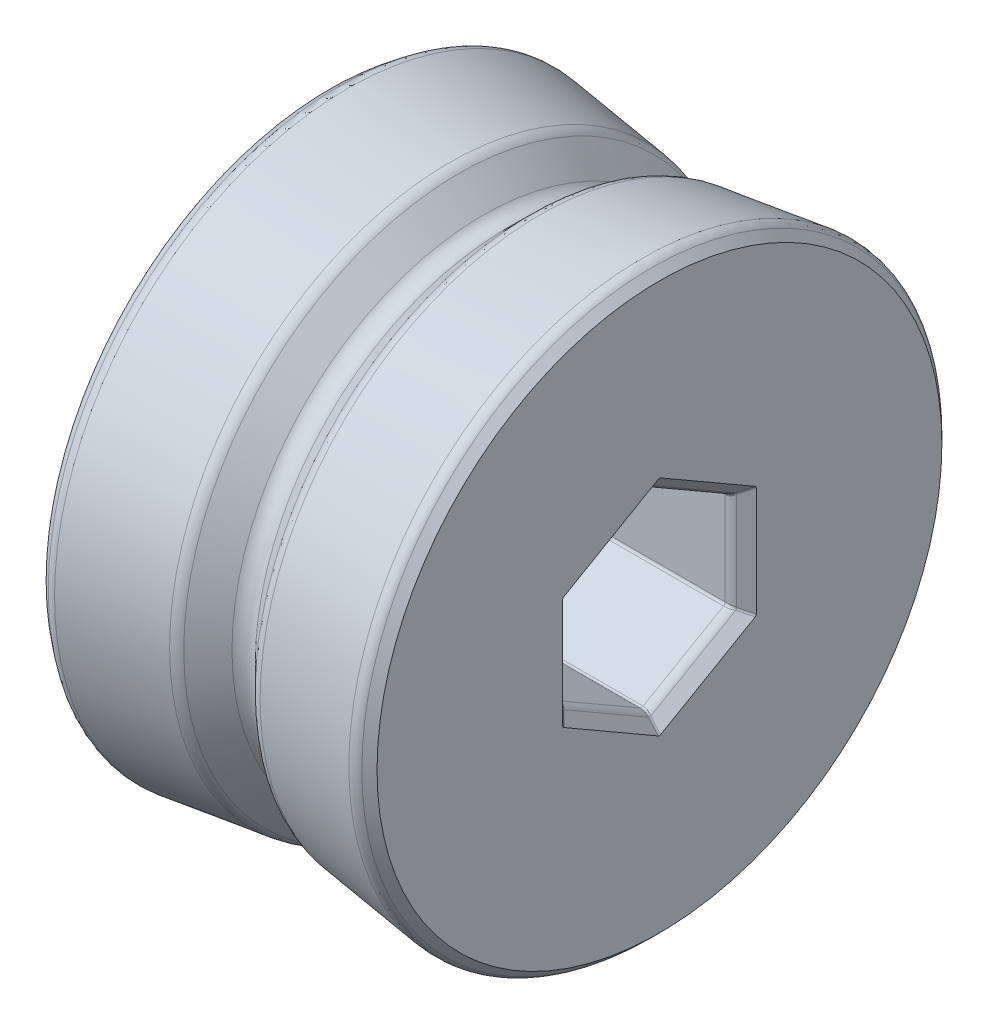
SolidWorks part; units mm, degrees
ref_plane "Front Plane" through (0, 0, 0) normal (0, 0, 1) x (1, 0, 0)
ref_plane "Top Plane" through (0, 0, 0) normal (0, 1, 0) x (1, 0, 0)
ref_plane "Right Plane" through (0, 0, 0) normal (1, 0, 0) x (0, 0, -1)
sketch "Sketch1" plane through (0, 0, 0) normal (0, 0, 1) x (1, 0, 0)
  line L0 (0, 0) -> (25.4, 0) construction
  line L1 (0, 0) -> (0, 22.7877)
  line L2 (0, 22.7877) -> (9.2118, 21.5749)
  line L3 (9.944, 21.2138) -> (11.802, 19.3558)
  line L4 (13.598, 19.3558) -> (15.456, 21.2138)
  line L5 (16.1882, 21.5749) -> (25.4, 22.7877)
  line L6 (25.4, 22.7877) -> (25.4, 0)
  line L7 (0, 22.7877) -> (25.4, 22.7877) construction
  line L8 (0, 0) -> (25.4, 0)
  circle A0 centre (12.7, 21.7805) radius 2.3495 construction
  arc A1 (15.456, 21.2138) -> (16.1882, 21.5749) centre (16.354, 20.3158) cw
  arc A2 (9.2118, 21.5749) -> (9.944, 21.2138) centre (9.046, 20.3158) cw
  arc A3 (11.802, 19.3558) -> (13.598, 19.3558) centre (12.7, 20.2539) ccw
  point P3 (12.7, 0)
  point P9 (12.7, 24.13)
  point P10 (0, 23.9923)
  point P11 (12.7, 19.7278)
  point P12 (25.4, 24.3537)
  point P13 (0, 0)
  point P16 (0, 0)
  point P17 (25.4, 22.9684)
  point P18 (9.9682, 21.1896)
  point P19 (0, 26.2811)
  point P20 (0, 0)
  point P21 (25.4, 22.7877)
  point P24 (15.7608, 21.5186)
  point P27 (9.6392, 21.5186)
  dimension "D1" = 4.699
  dimension "D5" = 1.27
  dimension "D2" = 25.4
  dimension "D3" = 24.13
  dimension "D4" = 82.5
revolve "Revolve1" add sketch "Sketch1" angle 360 about L8
sketch "Sketch2" plane through (25.4, 0, 0) normal (1, 0, 0) x (0, 0, -1)
  line L1 (6.45, -3.7239) -> (6.45, 3.7239)
  line L2 (6.45, 3.7239) -> (0, 7.4478)
  line L3 (0, 7.4478) -> (-6.45, 3.7239)
  line L4 (-6.45, 3.7239) -> (-6.45, -3.7239)
  line L5 (-6.45, -3.7239) -> (0, -7.4478)
  line L6 (0, -7.4478) -> (6.45, -3.7239)
  circle A0 centre (0, 0) radius 6.45 construction
  point P1 (6.45, 0)
  point P10 (0, 7.4478)
  dimension "D1" = 12.9
extrude "Cut-Extrude1" cut sketch "Sketch2" against normal through all both and the other way through all
chamfer "Chamfer1" distance 1.016 angle 45 14 edges at (0, 0, 6.45) (0, 5.5859, 3.225) (0, 5.5859, -3.225) (0, 0, -6.45) (0, -5.5859, -3.225) (0, -5.5859, 3.225) (25.4, 5.5859, -3.225) (25.4, 5.5859, 3.225) (25.4, 0, 6.45) (25.4, -5.5859, 3.225) (25.4, -5.5859, -3.225) (25.4, 0, -6.45) (0, 0, 22.7877) (25.4, 0, 22.7877)
fillet "Fillet2" radius 0.889 14 edges at (1.016, -5.5859, -3.225) (1.016, 0, -6.45) (1.016, 5.5859, -3.225) (1.016, 5.5859, 3.225) (1.016, 0, 6.45) (1.016, -5.5859, 3.225) (24.384, -5.5859, 3.225) (24.384, 0, 6.45) (24.384, 5.5859, 3.225) (24.384, 5.5859, -3.225) (24.384, 0, -6.45) (24.384, -5.5859, -3.225) (1.0073, 0, -22.655) (24.5022, 0, 22.6695)
fillet "Fillet3" radius 0.254 30 edges at (0.3778, -4.0924, -7.0882) (1.044, -3.763, -6.5177) (25.0222, -4.0924, -7.0882) (24.356, -3.763, -6.5177) (0.3778, -8.1847, 0) (1.044, -7.526, 0) (25.0222, -8.1847, 0) (24.356, -7.526, 0) (0.3778, 4.0924, 7.0882) (1.044, 3.763, 6.5177) (25.0222, 4.0924, 7.0882) (24.356, 3.763, 6.5177) (0.3778, 8.1847, 0) (1.044, 7.526, 0) (25.0222, 8.1847, 0) (24.356, 7.526, 0) (0.3778, 4.0924, -7.0882) (1.044, 3.763, -6.5177) (25.0222, 4.0924, -7.0882) (24.356, 3.763, -6.5177) (0.3778, -4.0924, 7.0882) (1.044, -3.763, 6.5177) (25.0222, -4.0924, 7.0882) (24.356, -3.763, 6.5177) (12.7, -3.7239, -6.45) (12.7, -7.4478, 0) (12.7, 3.7239, 6.45) (12.7, 7.4478, 0) (12.7, 3.7239, -6.45) (12.7, -3.7239, 6.45)
